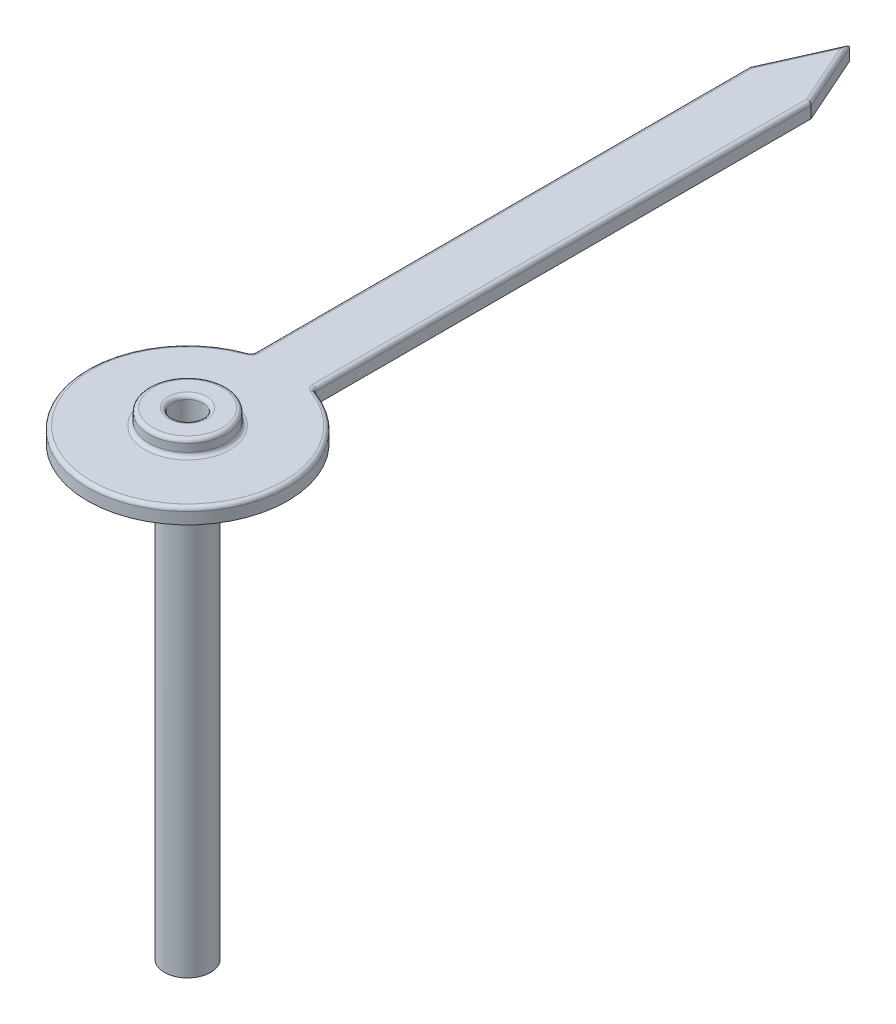
SolidWorks part; units mm, degrees
ref_plane "Front Plane" through (0, 0, 0) normal (0, 0, 1) x (1, 0, 0)
ref_plane "Top Plane" through (0, 0, 0) normal (0, 1, 0) x (1, 0, 0)
ref_plane "Right Plane" through (0, 0, 0) normal (1, 0, 0) x (0, 0, -1)
sketch "Sketch1" plane through (0, 0, 0) normal (0, 1, 0) x (1, 0, 0)
  line L35 (-86.3194, -39.0544) -> (-86.3194, -35.8249)
  line L36 (-86.7194, -39.0544) -> (-86.7194, -35.8249)
  line L37 (-86.5194, -35.3748) -> (-86.7194, -35.8249)
  line L38 (-86.3194, -35.8249) -> (-86.5194, -35.3748)
  circle A0 centre (-86.5194, -39.6725) radius 0.1
  arc A60 (-86.7194, -39.0544) -> (-86.3194, -39.0544) centre (-86.5194, -39.6725) ccw
  dimension "D1" = 0.2
extrude "Boss-Extrude1" add sketch "Sketch1" along normal blind 0.1
sketch "Sketch2" plane through (0, 0.1, 0) normal (0, 1, 0) x (1, 0, 0)
  circle A0 centre (-86.5194, -39.6725) radius 0.25
  circle A1 centre (-86.5194, -39.6725) radius 0.1
  dimension "D1" = 0.5
extrude "Boss-Extrude2" add sketch "Sketch2" along normal blind 0.1 and the other way blind 3
fillet "Fillet1" radius 0.025 2 edges at (-86.5194, 0.2, 39.7725) (-86.5194, 0.2, 39.9225)
fillet "Fillet2" radius 0.025 8 edges at (-86.3194, 0.1, 37.4397) (-86.5194, 0.1, 40.3222) (-86.7194, 0.1, 37.4397) (-86.6194, 0.1, 35.5999) (-86.4194, 0.1, 35.5999) (-86.5194, 0.1, 39.9225) (-86.7194, 0.05, 39.0544) (-86.3194, 0.05, 39.0544)
sketch "Sketch3" plane through (0, -2.9, 0) normal (0, -1, 0) x (1, 0, 0)
  circle A0 centre (-86.5194, 39.6725) radius 0.15
  circle A1 centre (-86.5194, 39.6725) radius 0.368
  dimension "D1" = 0.3
extrude "Cut-Extrude1" cut sketch "Sketch3" against normal up to surface (2.9 mm away) up to face at (-86.5194, 0, 39.9225)
